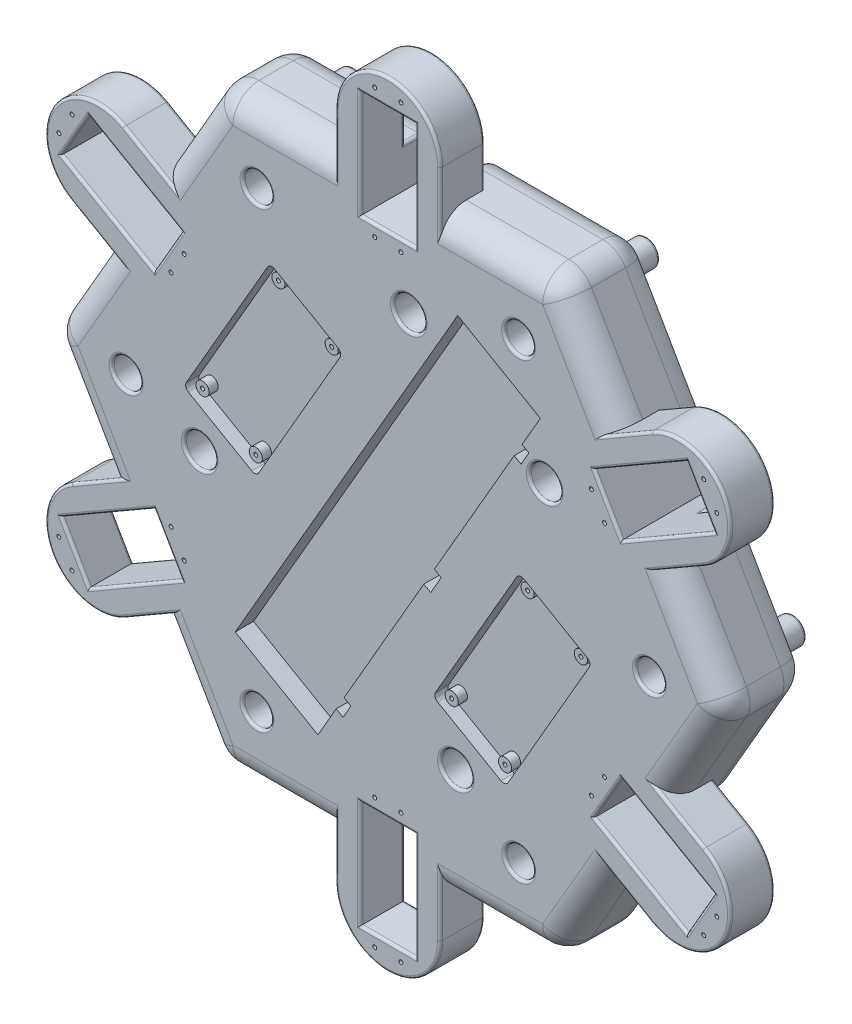
SolidWorks part; units mm, degrees
material "ABS"
ref_plane "Front Plane" through (0, 0, 0) normal (0, 0, 1) x (1, 0, 0)
ref_plane "Top Plane" through (0, 0, 0) normal (0, 1, 0) x (1, 0, 0)
ref_plane "Right Plane" through (0, 0, 0) normal (1, 0, 0) x (0, 0, -1)
sketch "HEXAGON" plane through (0, 0, 0) normal (0, 0, 1) x (1, 0, 0)
  line L96 (102.6779, -47.0398) -> (89.2545, -39.2898)
  line L99 (78.7545, -57.4763) -> (92.1779, -65.2263)
  line L102 (10.5, -112.383) -> (10.5, -96.883)
  line L105 (-10.5, -96.883) -> (-10.5, -112.383)
  line L108 (-78.7545, -57.4763) -> (-92.1779, -65.2263)
  line L111 (-102.6779, -47.0398) -> (-89.2545, -39.2898)
  line L114 (-89.2545, 39.5237) -> (-102.6779, 47.2737)
  line L117 (-78.7545, 57.7102) -> (-92.1779, 65.4602)
  line L148 (-64.9519, -112.383) -> (64.9519, -112.383)
  line L149 (-64.9519, -112.383) -> (-129.9038, 0.117)
  line L150 (-129.9038, 0.117) -> (-64.9519, 112.617)
  line L151 (129.9038, 0.117) -> (64.9519, -112.383)
  line L155 (92.1779, 65.4602) -> (78.7545, 57.7102)
  line L156 (89.2545, 39.5237) -> (102.6779, 47.2737)
  line L157 (78.7545, 57.7102) -> (89.2545, 39.5237)
  line L158 (64.9519, 112.617) -> (129.9038, 0.117)
  line L159 (-10.5, 112.617) -> (-10.5, 97.117)
  line L160 (10.5, 97.117) -> (10.5, 112.617)
  line L161 (10.5, 97.117) -> (-10.5, 97.117)
  line L162 (-64.9519, 112.617) -> (64.9519, 112.617)
  line L163 (89.2545, -39.2898) -> (78.7545, -57.4763)
  line L164 (10.5, -96.883) -> (-10.5, -96.883)
  line L165 (-78.7545, -57.4763) -> (-89.2545, -39.2898)
  line L166 (-89.2545, 39.5237) -> (-78.7545, 57.7102)
extrude "MBODY" add sketch "HEXAGON" along normal blind 33
sketch "BottomFloor" plane through (0, 0, 0) normal (0, 0, 1) x (1, 0, 0)
  line L24 (0, -112.383) -> (20, -112.383)
  line L29 (20, -112.383) -> (20, -82.383)
  line L82 (-87.4279, 73.6875) -> (-67.8387, 107.617)
  line L83 (20, -82.383) -> (-20, -82.383)
  line L84 (-20, -82.383) -> (-20, -112.383)
  line L85 (-20, -112.383) -> (0, -112.383)
  line L87 (97.4279, -56.133) -> (107.4279, -38.8125)
  line L88 (107.4279, -38.8125) -> (81.4471, -23.8125)
  line L89 (81.4471, -23.8125) -> (61.4471, -58.4535)
  line L90 (61.4471, -58.4535) -> (87.4279, -73.4535)
  line L91 (87.4279, -73.4535) -> (97.4279, -56.133)
  line L92 (-97.4279, -56.133) -> (-87.4279, -73.4535)
  line L93 (-87.4279, -73.4535) -> (-61.4471, -58.4535)
  line L94 (-61.4471, -58.4535) -> (-81.4471, -23.8125)
  line L95 (-81.4471, -23.8125) -> (-107.4279, -38.8125)
  line L96 (-107.4279, -38.8125) -> (-97.4279, -56.133)
  line L97 (-97.4279, 56.367) -> (-107.4279, 39.0465)
  line L98 (-107.4279, 39.0465) -> (-81.4471, 24.0465)
  line L99 (-81.4471, 24.0465) -> (-61.4471, 58.6875)
  line L100 (-61.4471, 58.6875) -> (-87.4279, 73.6875)
  line L101 (-87.4279, 73.6875) -> (-97.4279, 56.367)
  line L102 (0, 112.617) -> (20, 112.617)
  line L103 (20, 112.617) -> (20, 82.617)
  line L104 (20, 82.617) -> (-20, 82.617)
  line L105 (-20, 82.617) -> (-20, 112.617)
  line L106 (-20, 112.617) -> (0, 112.617)
  line L107 (97.4279, 56.367) -> (87.4279, 73.6875)
  line L108 (87.4279, 73.6875) -> (61.4471, 58.6875)
  line L109 (61.4471, 58.6875) -> (81.4471, 24.0465)
  line L110 (81.4471, 24.0465) -> (107.4279, 39.0465)
  line L111 (107.4279, 39.0465) -> (97.4279, 56.367)
  line L112 (-59.1784, 112.617) -> (-20, 112.617)
  line L113 (20, 112.617) -> (59.1784, 112.617)
  line L114 (67.8387, 107.617) -> (87.4279, 73.6875)
  line L115 (107.4279, 39.0465) -> (127.0171, 5.117)
  line L116 (127.0171, -4.883) -> (107.4279, -38.8125)
  line L117 (87.4279, -73.4535) -> (67.8387, -107.383)
  line L118 (10.5, -112.383) -> (64.9519, -112.383) construction
  line L119 (59.1784, -112.383) -> (20, -112.383)
  line L120 (-20, -112.383) -> (-59.1784, -112.383)
  line L121 (-67.8387, -107.383) -> (-87.4279, -73.4535)
  line L122 (-107.4279, -38.8125) -> (-127.0171, -4.883)
  line L123 (-127.0171, 5.117) -> (-107.4279, 39.0465)
  line L124 (64.9519, 112.617) -> (59.1784, 102.617)
  line L125 (59.1784, 102.617) -> (56.0184, 97.1437)
  line L126 (129.9038, 0.117) -> (118.3568, 0.117)
  line L127 (118.3568, 0.117) -> (112.0368, 0.117)
  line L128 (-64.9519, 112.617) -> (-59.1784, 102.617)
  line L129 (-59.1784, 102.617) -> (-56.0184, 97.1437)
  line L130 (64.9519, -112.383) -> (59.1784, -102.383)
  line L131 (59.1784, -102.383) -> (56.0184, -96.9098)
  line L132 (-129.9038, 0.117) -> (-118.3568, 0.117)
  line L133 (-118.3568, 0.117) -> (-112.0368, 0.117)
  line L134 (-64.9519, -112.383) -> (-59.1784, -102.383)
  line L135 (-59.1784, -102.383) -> (-56.0184, -96.9098)
  arc A0 (-127.0171, 5.117) -> (-127.0171, -4.883) centre (-118.3568, 0.117) ccw
  arc A1 (-67.8387, -107.383) -> (-59.1784, -112.383) centre (-59.1784, -102.383) ccw
  arc A2 (59.1784, -112.383) -> (67.8387, -107.383) centre (59.1784, -102.383) ccw
  arc A3 (127.0171, -4.883) -> (127.0171, 5.117) centre (118.3568, 0.117) ccw
  arc A4 (67.8387, 107.617) -> (59.1784, 112.617) centre (59.1784, 102.617) ccw
  arc A5 (-59.1784, 112.617) -> (-67.8387, 107.617) centre (-59.1784, 102.617) ccw
  circle A6 centre (-56.0184, -96.9098) radius 5
  circle A7 centre (56.0184, -96.9098) radius 5
  circle A8 centre (112.0368, 0.117) radius 5
  circle A9 centre (56.0184, 97.1437) radius 5
  circle A10 centre (-56.0184, 97.1437) radius 5
  circle A11 centre (-112.0368, 0.117) radius 5
  point P45 (-129.9038, 0.117)
  point P48 (-64.9519, -112.383)
  point P51 (64.9519, -112.383)
  point P54 (129.9038, 0.117)
  point P57 (64.9519, 112.617)
  point P60 (-64.9519, 112.617)
  dimension "D1" = 10
extrude "BODYBASE" add sketch "BottomFloor" against normal blind 10
sketch "CircleBits" plane through (0, 0, 33) normal (0, 0, 1) x (1, 0, 0)
  line L4 (-87.4279, -73.4535) -> (-100.8513, -81.2035)
  line L22 (-20, 112.617) -> (-20, 128.117)
  line L24 (20, 112.617) -> (10.5, 112.617)
  line L26 (10.5, 112.617) -> (10.5, 138.117)
  line L27 (10.5, 138.117) -> (-10.5, 138.117)
  line L28 (-10.5, 138.117) -> (-10.5, 112.617)
  line L43 (-20, 112.617) -> (-10.5, 112.617)
  line L44 (20, -112.383) -> (20, -127.883)
  line L45 (87.4279, 73.6875) -> (100.8513, 81.4375)
  line L46 (107.4279, 39.0465) -> (120.8513, 46.7965)
  line L47 (107.4279, 39.0465) -> (102.6779, 47.2737)
  line L48 (102.6779, 47.2737) -> (124.7615, 60.0237)
  line L49 (124.7615, 60.0237) -> (114.2615, 78.2102)
  line L50 (114.2615, 78.2102) -> (92.1779, 65.4602)
  line L51 (87.4279, 73.6875) -> (92.1779, 65.4602)
  line L52 (-20, -112.383) -> (-20, -127.883)
  line L53 (-20, -112.383) -> (-10.5, -112.383)
  line L54 (-10.5, -112.383) -> (-10.5, -137.883)
  line L55 (-10.5, -137.883) -> (10.5, -137.883)
  line L56 (10.5, -137.883) -> (10.5, -112.383)
  line L57 (20, -112.383) -> (10.5, -112.383)
  line L58 (107.4279, -38.8125) -> (120.8513, -46.5625)
  line L59 (87.4279, -73.4535) -> (100.8513, -81.2035)
  line L60 (87.4279, -73.4535) -> (92.1779, -65.2263)
  line L61 (92.1779, -65.2263) -> (114.2615, -77.9763)
  line L62 (114.2615, -77.9763) -> (124.7615, -59.7898)
  line L63 (124.7615, -59.7898) -> (102.6779, -47.0398)
  line L64 (107.4279, -38.8125) -> (102.6779, -47.0398)
  line L65 (-107.4279, -38.8125) -> (-120.8513, -46.5625)
  line L66 (-107.4279, -38.8125) -> (-102.6779, -47.0398)
  line L67 (-102.6779, -47.0398) -> (-124.7615, -59.7898)
  line L68 (-124.7615, -59.7898) -> (-114.2615, -77.9763)
  line L69 (-114.2615, -77.9763) -> (-92.1779, -65.2263)
  line L70 (-87.4279, -73.4535) -> (-92.1779, -65.2263)
  line L71 (-107.4279, 39.0465) -> (-120.8513, 46.7965)
  line L72 (-87.4279, 73.6875) -> (-100.8513, 81.4375)
  line L73 (-87.4279, 73.6875) -> (-92.1779, 65.4602)
  line L74 (-92.1779, 65.4602) -> (-114.2615, 78.2102)
  line L75 (-114.2615, 78.2102) -> (-124.7615, 60.0237)
  line L76 (-124.7615, 60.0237) -> (-102.6779, 47.2737)
  line L77 (-107.4279, 39.0465) -> (-102.6779, 47.2737)
  line L80 (20, 128.117) -> (20, 112.617)
  arc A6 (100.8513, 81.4375) -> (120.8513, 46.7965) centre (110.8513, 64.117) cw
  arc A7 (20, -127.883) -> (-20, -127.883) centre (0, -127.883) cw
  arc A8 (120.8513, -46.5625) -> (100.8513, -81.2035) centre (110.8513, -63.883) cw
  arc A9 (-100.8513, -81.2035) -> (-120.8513, -46.5625) centre (-110.8513, -63.883) cw
  arc A10 (-120.8513, 46.7965) -> (-100.8513, 81.4375) centre (-110.8513, 64.117) cw
  arc A11 (-20, 128.117) -> (20, 128.117) centre (0, 128.117) cw
extrude "SERVOCIRCLE" add sketch "CircleBits" against normal blind 17
sketch "Breadboard" plane through (0, 0, 33) normal (0, 0, 1) x (1, 0, 0)
  line L1 (-26.695, -82.7372) -> (-58.305, -64.4872)
  line L3 (-58.305, -64.4872) -> (26.695, 82.7372)
  line L4 (58.305, 64.4872) -> (26.695, 82.7372)
  line L5 (58.305, 64.4872) -> (57.305, 62.7551)
  line L6 (57.305, 62.7551) -> (65.9652, 57.7551)
  line L10 (-16.695, -65.4167) -> (13.805, -12.5891)
  line L13 (51.305, 52.3628) -> (53.903, 50.8628)
  line L14 (53.903, 50.8628) -> (50.903, 45.6667)
  line L15 (50.903, 45.6667) -> (48.305, 47.1667)
  line L18 (16.403, -14.0891) -> (13.805, -12.5891)
  line L19 (-16.695, -65.4167) -> (-14.097, -66.9167)
  line L20 (-14.097, -66.9167) -> (-17.097, -72.1128)
  line L21 (-17.097, -72.1128) -> (-19.695, -70.6128)
  line L24 (-26.695, -82.7372) -> (-25.695, -81.0051)
  line L25 (-25.695, -81.0051) -> (-17.0348, -86.0051)
  line L26 (57.305, 62.7551) -> (51.305, 52.3628)
  line L27 (-25.695, -81.0051) -> (-19.695, -70.6128)
  line L29 (20.403, -7.1609) -> (17.805, -5.6609)
  line L30 (17.805, -5.6609) -> (48.305, 47.1667)
  line L31 (16.403, -14.0891) -> (20.403, -7.1609)
  point P0 (-15.805, 9.125)
extrude "BBCUT" cut sketch "Breadboard" against normal blind 7 contours L24 L1 L3 L4 L5 L26 L13 L14 L15 L30 L29 L31 L18 L10 L19 L20 L21 L27
sketch "Sketch9" plane through (0, 0, 33) normal (0, 0, 1) x (1, 0, 0)
  line L5 (76.2298, -5.7892) -> (51.9811, 8.2108)
  line L6 (-43.251, 63.1456) -> (-19.0023, 49.1456)
  line L8 (18.9811, -48.9469) -> (43.2298, -62.9469)
  line L11 (-45.983, 62.4136) -> (-76.983, 8.72)
  line L12 (-76.251, 5.9879) -> (-52.0023, -8.0121)
  line L13 (-18.2702, 46.4136) -> (-49.2702, -7.28)
  line L14 (76.9618, -8.5212) -> (45.9618, -62.2148)
  line L15 (49.249, 7.4788) -> (18.249, -46.2148)
  arc A6 (-76.983, 8.72) -> (-76.251, 5.9879) centre (-75.251, 7.72) ccw
  arc A7 (-52.0023, -8.0121) -> (-49.2702, -7.28) centre (-51.0023, -6.28) ccw
  arc A8 (-18.2702, 46.4136) -> (-19.0023, 49.1456) centre (-20.0023, 47.4136) ccw
  arc A9 (-43.251, 63.1456) -> (-45.983, 62.4136) centre (-44.251, 61.4136) ccw
  arc A10 (18.249, -46.2148) -> (18.9811, -48.9469) centre (19.9811, -47.2148) ccw
  arc A11 (43.2298, -62.9469) -> (45.9618, -62.2148) centre (44.2298, -61.2148) ccw
  arc A12 (76.9618, -8.5212) -> (76.2298, -5.7892) centre (75.2298, -7.5212) ccw
  arc A13 (51.9811, 8.2108) -> (49.249, 7.4788) centre (50.9811, 6.4788) ccw
  point P7 (44.9618, -63.9469)
  point P11 (77.9618, -6.7892)
  dimension "D1" = 2
  dimension "D2" = 2
extrude "PCACUT" cut sketch "Sketch9" against normal blind 5 contours L5 A13 L15 A10 L8 A11 L14 A12 | L11 A6 L12 A7 L13 A8 L6 A9
sketch "Sketch10" plane through (0, 0, 28) normal (0, 0, 1) x (1, 0, 0)
  circle A0 centre (22.9296, -46.6078) radius 0.75
  circle A1 centre (43.2812, -58.3578) radius 0.75
  circle A2 centre (51.9296, 3.6217) radius 0.75
  circle A3 centre (72.2812, -8.1283) radius 0.75
  circle A4 centre (51.9296, 3.6217) radius 2.5
  circle A5 centre (72.2812, -8.1283) radius 2.5
  circle A6 centre (43.2812, -58.3578) radius 2.5
  circle A7 centre (22.9296, -46.6078) radius 2.5
  circle A8 centre (-72.3024, 8.327) radius 0.75
  circle A9 centre (-51.9508, -3.423) radius 0.75
  circle A10 centre (-43.3024, 58.5565) radius 0.75
  circle A11 centre (-22.9508, 46.8065) radius 0.75
  circle A12 centre (-43.3024, 58.5565) radius 2.5
  circle A13 centre (-22.9508, 46.8065) radius 2.5
  circle A14 centre (-51.9508, -3.423) radius 2.5
  circle A15 centre (-72.3024, 8.327) radius 2.5
extrude "PCAFIXTURE" add sketch "Sketch10" along normal blind 3.5 contours A0 | A2 | A4 | A3 | A5 | A1 | A6 | A7 | A12 | A10 | A13 | A11 | A14 | A9 | A15 | A8
sketch "Sketch16" plane through (0, 0, 0) normal (0, 0, -1) x (-1, 0, 0)
  line L0 (-47.6314, -82.383) -> (-61.4471, -58.4535)
  line L1 (-61.4471, -58.4535) -> (-81.4471, -23.8125)
  line L2 (-20, -82.383) -> (-47.6314, -82.383)
  line L3 (81.4471, -23.8125) -> (95.2628, 0.117)
  line L4 (-81.4471, 24.0465) -> (-61.4471, 58.6875)
  line L5 (-20, 82.617) -> (20, 82.617)
  line L6 (61.4471, 58.6875) -> (81.4471, 24.0465)
  line L7 (81.4471, -23.8125) -> (61.4471, -58.4535)
  line L10 (20, -82.383) -> (-20, -82.383)
  line L11 (47.6314, 82.617) -> (20, 82.617)
  line L12 (-20, 82.617) -> (-47.6314, 82.617)
  line L13 (-95.2628, 0.117) -> (-81.4471, -23.8125)
  line L14 (20, -82.383) -> (47.6314, -82.383)
  line L15 (-61.4471, 58.6875) -> (-47.6314, 82.617)
  line L16 (-81.4471, 24.0465) -> (-95.2628, 0.117)
  line L17 (61.4471, 58.6875) -> (47.6314, 82.617)
  line L18 (81.4471, 24.0465) -> (95.2628, 0.117)
  line L19 (61.4471, -58.4535) -> (47.6314, -82.383)
extrude "HOLLOWBOTTOM" cut sketch "Sketch16" against normal blind 18
sketch "Sketch18" plane through (0, 0, 18) normal (0, 0, 1) x (1, 0, 0)
  line L2 (31.3301, 44.3823) -> (37.8253, 40.6323)
  line L3 (37.8253, 40.6323) -> (40.3253, 44.9625)
  line L7 (-10.6699, -28.3638) -> (31.3301, 44.3823)
  line L9 (72.0333, 20.8823) -> (30.0333, -51.8638)
  line L10 (-68.8352, -35.1091) -> (3.9109, -77.1091)
  line L12 (40.3253, 44.9625) -> (47.2535, 40.9625)
  line L17 (-10.6699, -28.3638) -> (-4.1747, -32.1138)
  line L21 (2.7535, -36.1138) -> (0.2535, -40.4439)
  line L22 (0.2535, -40.4439) -> (-6.6747, -36.4439)
  line L23 (-6.6747, -36.4439) -> (-4.1747, -32.1138)
  line L29 (47.2535, 40.9625) -> (44.7535, 36.6323)
  line L30 (72.0333, 20.8823) -> (65.5381, 24.6323)
  line L31 (65.5381, 24.6323) -> (68.0381, 28.9625)
  line L32 (68.0381, 28.9625) -> (61.1099, 32.9625)
  line L33 (61.1099, 32.9625) -> (58.6099, 28.6323)
  line L35 (0, 0.117) -> (-15, -25.8638)
  line L39 (30.0333, -51.8638) -> (23.5381, -48.1138)
  line L40 (23.5381, -48.1138) -> (21.0381, -52.4439)
  line L41 (21.0381, -52.4439) -> (14.1099, -48.4439)
  line L42 (14.1099, -48.4439) -> (16.6099, -44.1138)
  line L43 (16.6099, -44.1138) -> (2.7535, -36.1138)
  line L44 (44.7535, 36.6323) -> (58.6099, 28.6323)
  line L51 (-18.0541, 72.846) -> (-11.5589, 69.096)
  line L52 (-11.5589, 69.096) -> (-9.0589, 73.4262)
  line L53 (-60.0541, 0.0999) -> (-18.0541, 72.846)
  line L54 (22.6491, 49.346) -> (-19.3509, -23.4001)
  line L55 (-9.0589, 73.4262) -> (-2.1307, 69.4262)
  line L56 (-60.0541, 0.0999) -> (-53.5589, -3.6501)
  line L57 (-46.6307, -7.6501) -> (-49.1307, -11.9802)
  line L58 (-49.1307, -11.9802) -> (-56.0589, -7.9802)
  line L59 (-56.0589, -7.9802) -> (-53.5589, -3.6501)
  line L60 (-2.1307, 69.4262) -> (-4.6307, 65.096)
  line L61 (22.6491, 49.346) -> (16.1539, 53.096)
  line L62 (16.1539, 53.096) -> (18.6539, 57.4262)
  line L63 (18.6539, 57.4262) -> (11.7257, 61.4262)
  line L64 (11.7257, 61.4262) -> (9.2257, 57.096)
  line L65 (-19.3509, -23.4001) -> (-25.8461, -19.6501)
  line L66 (-25.8461, -19.6501) -> (-28.3461, -23.9802)
  line L67 (-28.3461, -23.9802) -> (-35.2743, -19.9802)
  line L68 (-35.2743, -19.9802) -> (-32.7743, -15.6501)
  line L69 (-32.7743, -15.6501) -> (-46.6307, -7.6501)
  line L70 (-4.6307, 65.096) -> (9.2257, 57.096)
  line L71 (16.6161, -65.1031) -> (12.2859, -62.6031)
  line L72 (-60.4602, -20.6031) -> (-56.5852, -13.8915)
  line L73 (-64.9602, -28.3974) -> (-68.8352, -35.1091)
  line L74 (-60.4602, -20.6031) -> (-64.7903, -18.1031)
  line L75 (12.2859, -62.6031) -> (16.1609, -55.8915)
  line L76 (-27.4757, -47.5893) -> (-28.4757, -49.3214)
  line L77 (-64.7903, -18.1031) -> (-69.2903, -25.8974)
  line L78 (-69.2903, -25.8974) -> (-64.9602, -28.3974)
  line L81 (16.6161, -65.1031) -> (12.1161, -72.8974)
  line L82 (12.1161, -72.8974) -> (7.7859, -70.3974)
  line L83 (7.7859, -70.3974) -> (3.9109, -77.1091)
  line L84 (47.6314, 82.617) -> (-47.6314, -82.383)
  line L85 (-47.6314, -82.383) -> (-95.2628, 0.117) construction
  line L86 (47.6314, -82.383) -> (-47.6314, -82.383) construction
  line L87 (-71.4471, 41.367) -> (71.4471, -41.133)
  line L88 (-95.2628, 0.117) -> (-47.6314, 82.617) construction
  line L89 (95.2628, 0.117) -> (47.6314, -82.383) construction
  line L90 (16.1609, -55.8915) -> (-56.5852, -13.8915)
  point P73 (-67.0403, -22.0003)
  point P78 (14.3661, -69.0003)
extrude "BOTTOMBATTCUT" cut sketch "Sketch18" along normal blind 2 contours L81 L82 L83 L10 L73 L78 L77 L74 L72 L90 L75 L71 | L51 L52 L55 L60 L70 L64 L63 L62 L61 L54 L65 L66 L67 L68 L69 L57 L58 L59 L56 L53 | L2 L3 L12 L29 L44 L33 L32 L31 L30 L9 L39 L40 L41 L42 L43 L21 L22 L23 L17 L7
sketch "Sketch20" plane through (0, 0, 20) normal (0, 0, -1) x (-1, 0, 0)
  line L0 (-30.6817, -3.7407) -> (-48.0022, -13.7407)
  line L1 (30.8371, -53.2945) -> (6.6534, -67.257)
  line L2 (-23.2676, -63.7472) -> (-11.4832, -56.9435)
  line L3 (20.4621, -35.3245) -> (32.4621, -56.1091)
  line L4 (67.0403, -22.0003) -> (-14.3661, -69.0003)
  line L5 (-30.6817, -3.7407) -> (-13.3612, 6.2593)
  line L6 (64.7903, -18.1031) -> (69.2903, -25.8974) construction
  line L7 (-48.0022, -13.7407) -> (-61.9647, 10.443)
  line L8 (-13.3612, 6.2593) -> (0.6013, -17.9245)
  line L9 (-13.3612, 6.2593) -> (-27.3237, 30.443)
  line L10 (-27.3237, 30.443) -> (-32.5987, 39.5796)
  line L11 (30.8371, -53.2945) -> (21.8371, -37.706)
  line L12 (21.8371, -37.706) -> (46.0209, -23.7435)
  line L13 (-16.6161, -65.1031) -> (-12.1161, -72.8974) construction
  line L15 (18.7025, 24.723) -> (1.382, 14.723)
  line L16 (18.7025, 24.723) -> (36.023, 34.723)
  line L17 (1.382, 14.723) -> (-12.5805, 38.9067)
  line L18 (36.023, 34.723) -> (49.9855, 10.5392)
  line L19 (36.023, 34.723) -> (22.0605, 58.9067)
  line L20 (22.0605, 58.9067) -> (16.7855, 68.0433)
  line L22 (21.8371, -37.706) -> (-23.2676, -63.7472)
  line L23 (68.8352, -35.1091) -> (-3.9109, -77.1091) construction
  line L24 (39.7025, -11.6501) -> (-2.2975, 61.096)
  line L25 (32.7743, -15.6501) -> (46.6307, -7.6501) construction
  line L26 (4.6307, 65.096) -> (-9.2257, 57.096) construction
  line L27 (-51.6817, 32.6323) -> (-9.6817, -40.1138)
  line L28 (-44.7535, 36.6323) -> (-58.6099, 28.6323) construction
  line L29 (-16.6099, -44.1138) -> (-2.7535, -36.1138) construction
  line L30 (-51.0333, -15.4907) -> (-10.3301, 8.0093)
  line L31 (-72.0333, 20.8823) -> (-30.0333, -51.8638) construction
  line L32 (10.6699, -28.3638) -> (-31.3301, 44.3823) construction
  line L33 (-1.6491, 12.973) -> (39.0541, 36.473)
  line L34 (-22.6491, 49.346) -> (19.3509, -23.4001) construction
  line L35 (60.0541, 0.0999) -> (18.0541, 72.846) construction
  circle A0 centre (0.6013, -17.9245) radius 2
  circle A1 centre (-61.9647, 10.443) radius 2
  circle A2 centre (-32.5987, 39.5796) radius 0.8
  circle A3 centre (49.9855, 10.5392) radius 2
  circle A4 centre (-12.5805, 38.9067) radius 2
  circle A5 centre (16.7855, 68.0433) radius 0.8
  circle A6 centre (-11.4832, -56.9435) radius 0.8
  circle A7 centre (6.6534, -67.257) radius 2
  circle A8 centre (46.0209, -23.7435) radius 2
extrude "BOTTOMBATTFIXTURE" cut sketch "Sketch20" against normal blind 3.45 contours A6 | A7 | A0 | A1 | A2 | A8 | A5 | A4 | A3
sketch "Sketch33" plane through (0, 0, 20) normal (0, 0, -1) x (1, 0, 0)
  line L0 (30.6817, 3.7407) -> (48.0022, 13.7407)
  line L1 (-30.8371, 53.2945) -> (-6.6534, 67.257)
  line L2 (23.2676, 63.7472) -> (11.4832, 56.9435)
  line L3 (-20.4621, 35.3245) -> (-32.2121, 55.6761)
  line L4 (-66.6073, 22.2503) -> (13.9331, 68.7503)
  line L5 (30.6817, 3.7407) -> (13.3612, -6.2593)
  line L6 (48.0022, 13.7407) -> (61.9647, -10.443)
  line L7 (13.3612, -6.2593) -> (-0.6013, 17.9245)
  line L8 (13.3612, -6.2593) -> (27.3237, -30.443)
  line L9 (27.3237, -30.443) -> (32.5987, -39.5796)
  line L10 (-30.8371, 53.2945) -> (-21.8371, 37.706)
  line L11 (-21.8371, 37.706) -> (-46.0209, 23.7435)
  line L12 (-18.7025, -24.723) -> (-1.382, -14.723)
  line L13 (-18.7025, -24.723) -> (-36.023, -34.723)
  line L14 (-1.382, -14.723) -> (12.5805, -38.9067)
  line L15 (-36.023, -34.723) -> (-49.9855, -10.5392)
  line L16 (-36.023, -34.723) -> (-22.0605, -58.9067)
  line L17 (-22.0605, -58.9067) -> (-16.7855, -68.0433)
  line L18 (-21.8371, 37.706) -> (23.2676, 63.7472)
  line L19 (-39.4525, 11.2171) -> (2.0475, -60.663)
  line L20 (51.4317, -32.1993) -> (9.9317, 39.6808)
  line L21 (50.6003, 15.2407) -> (10.7631, -7.7593)
  line L22 (1.2161, -13.223) -> (-38.6211, -36.223)
  circle A0 centre (-0.6013, 17.9245) radius 2
  circle A1 centre (61.9647, -10.443) radius 2
  circle A2 centre (32.5987, -39.5796) radius 0.785
  circle A3 centre (-49.9855, -10.5392) radius 2
  circle A4 centre (12.5805, -38.9067) radius 2
  circle A5 centre (-16.7855, -68.0433) radius 0.785
  circle A6 centre (11.4832, 56.9435) radius 0.785
  circle A7 centre (-6.6534, 67.257) radius 2
  circle A8 centre (-46.0209, 23.7435) radius 2
  circle A9 centre (-6.6534, 67.257) radius 1.5
  circle A10 centre (-46.0209, 23.7435) radius 1.5
  circle A11 centre (-49.9855, -10.5392) radius 1.5
  circle A12 centre (12.5805, -38.9067) radius 1.5
  circle A13 centre (61.9647, -10.443) radius 1.5
  circle A14 centre (-0.6013, 17.9245) radius 1.5
extrude "BOTTOMBATTFIXTURE1" add sketch "Sketch33" against normal blind 1.75 contours A8 | A10 | A3 | A11 | A4 | A12 | A1 | A13 | A0 | A14 | A7 | A9
fillet "BOTTOMBATTFIXTURE2" radius 0.8 6 edges at (11.0805, 38.9067, 20) (60.4647, 10.443, 20) (-51.4855, 10.5392, 20) (-2.1013, -17.9245, 20) (-47.5209, -23.7435, 20) (-8.1534, -67.257, 20)
sketch "Sketch26" plane through (0, 0, 33) normal (0, 0, 1) x (1, 0, 0)
  line L0 (5, -142.133) -> (5, -137.383)
  line L1 (114.2615, 78.2102) -> (89.2545, 39.5237)
  line L2 (-5, -137.383) -> (-5, -142.133)
  line L3 (-5, -142.133) -> (5, -142.133)
  line L4 (5, -92.633) -> (-5, -92.633)
  line L5 (114.2615, -77.9763) -> (89.2545, -39.2898)
  line L6 (5, -97.383) -> (5, -92.633)
  line L7 (-5, -97.383) -> (-10, -97.383)
  line L8 (10.5, -96.883) -> (-10.5, -137.883)
  line L9 (-5, -97.383) -> (-5, -92.633)
  line L10 (125.6921, -66.6779) -> (121.5785, -64.3029)
  line L11 (116.5785, -72.9632) -> (120.6921, -75.3382)
  line L12 (120.6921, -75.3382) -> (125.6921, -66.6779)
  line L13 (82.8239, -41.9279) -> (77.8239, -50.5882)
  line L14 (86.9375, -44.3029) -> (82.8239, -41.9279)
  line L15 (81.9375, -52.9632) -> (79.4375, -57.2933)
  line L16 (81.9375, -52.9632) -> (77.8239, -50.5882)
  line L17 (120.6921, 75.5721) -> (116.5785, 73.1971)
  line L18 (121.5785, 64.5368) -> (125.6921, 66.9118)
  line L19 (125.6921, 66.9118) -> (120.6921, 75.5721)
  line L20 (77.8239, 50.8221) -> (82.8239, 42.1618)
  line L21 (-78.7545, -57.4763) -> (-124.7615, -59.7898)
  line L22 (86.9375, 44.5368) -> (89.4375, 40.2067)
  line L23 (86.9375, 44.5368) -> (82.8239, 42.1618)
  line L24 (-5, 142.367) -> (-5, 137.617)
  line L25 (5, 137.617) -> (5, 142.367)
  line L26 (5, 142.367) -> (-5, 142.367)
  line L27 (-5, 92.867) -> (5, 92.867)
  line L28 (-5, 97.617) -> (-5, 92.867)
  line L29 (5, 97.617) -> (10, 97.617)
  line L30 (5, 97.617) -> (5, 92.867)
  line L31 (-125.6921, 66.9118) -> (-121.5785, 64.5368)
  line L32 (-116.5785, 73.1971) -> (-120.6921, 75.5721)
  line L33 (-120.6921, 75.5721) -> (-125.6921, 66.9118)
  line L34 (-82.8239, 42.1618) -> (-77.8239, 50.8221)
  line L35 (-86.9375, 44.5368) -> (-82.8239, 42.1618)
  line L36 (-81.9375, 53.1971) -> (-79.4375, 57.5272)
  line L37 (-81.9375, 53.1971) -> (-77.8239, 50.8221)
  line L38 (-120.6921, -75.3382) -> (-116.5785, -72.9632)
  line L39 (-121.5785, -64.3029) -> (-125.6921, -66.6779)
  line L40 (-125.6921, -66.6779) -> (-120.6921, -75.3382)
  line L41 (-77.8239, -50.5882) -> (-82.8239, -41.9279)
  line L42 (-81.9375, -52.9632) -> (-77.8239, -50.5882)
  line L43 (-86.9375, -44.3029) -> (-89.4375, -39.9728)
  line L44 (-86.9375, -44.3029) -> (-82.8239, -41.9279)
  line L45 (-89.2545, 39.5237) -> (-114.2615, 78.2102)
  line L46 (77.8239, 50.8221) -> (125.6921, 66.9118)
  line L47 (77.8239, -50.5882) -> (125.6921, -66.6779)
  line L48 (-5, -92.633) -> (5, -142.133)
  line L49 (-82.8239, -41.9279) -> (-120.6921, -75.3382)
  line L50 (-125.6921, 66.9118) -> (-77.8239, 50.8221)
  line L51 (101.758, 58.867) -> (99.9279, 62.0368)
  line L52 (101.758, -58.633) -> (99.9279, -61.8029)
  line L53 (0, -117.383) -> (-3.3849, -117.383)
  line L54 (-101.758, -58.633) -> (-103.7411, -55.4995)
  line L55 (-101.758, 58.867) -> (-99.3191, 62.0406)
  circle A24 centre (-125.6921, -66.6779) radius 0.75
  circle A25 centre (-120.6921, -75.3382) radius 0.75
  circle A26 centre (-82.8239, -41.9279) radius 0.75
  circle A27 centre (-77.8239, -50.5882) radius 0.75
  circle A28 centre (-5, -92.633) radius 0.75
  circle A29 centre (5, -92.633) radius 0.75
  circle A30 centre (-5, -142.133) radius 0.75
  circle A31 centre (5, -142.133) radius 0.75
  circle A32 centre (125.6921, -66.6779) radius 0.75
  circle A33 centre (120.6921, -75.3382) radius 0.75
  circle A34 centre (77.8239, -50.5882) radius 0.75
  circle A35 centre (82.8239, -41.9279) radius 0.75
  circle A36 centre (125.6921, 66.9118) radius 0.75
  circle A37 centre (120.6921, 75.5721) radius 0.75
  circle A38 centre (77.8239, 50.8221) radius 0.75
  circle A39 centre (82.8239, 42.1618) radius 0.75
  circle A40 centre (5, 92.867) radius 0.75
  circle A41 centre (-5, 92.867) radius 0.75
  circle A42 centre (5, 142.367) radius 0.75
  circle A43 centre (-5, 142.367) radius 0.75
  circle A45 centre (-125.6921, 66.9118) radius 0.75
  circle A46 centre (-77.8239, 50.8221) radius 0.75
  circle A47 centre (-82.8239, 42.1618) radius 0.75
  circle A48 centre (-120.6921, 75.5721) radius 0.75
sketch "Sketch28" plane through (0, 0, 18) normal (0, 0, -1) x (-1, 0, 0)
  line L6 (-19.1382, -69.7347) -> (-27.7984, -74.7347)
  line L7 (65.0624, -9.5745) -> (73.7227, -4.5745)
  line L11 (-27.7984, -74.7347) -> (-32.7984, -66.0745)
  line L12 (-32.7984, -66.0745) -> (-24.1382, -61.0745)
  line L14 (78.7227, -13.2347) -> (70.0624, -18.2347)
  line L15 (70.0624, -18.2347) -> (65.0624, -9.5745)
  line L22 (-6.1684, 80.8005) -> (-14.8286, 75.8005)
  line L23 (-14.8286, 75.8005) -> (-9.8286, 67.1403)
  line L24 (-1.1684, 72.1403) -> (-9.8286, 67.1403)
  line L27 (-58.1506, 50.8368) -> (-66.8109, 45.8368)
  line L28 (-66.8109, 45.8368) -> (-61.8109, 37.1766)
  line L29 (-53.1506, 42.1766) -> (-61.8109, 37.1766)
  circle A0 centre (-7.9985, 73.9704) radius 6
  circle A1 centre (-59.9599, 43.9705) radius 6
  circle A2 centre (-25.9683, -67.9046) radius 6
  circle A3 centre (71.8926, -11.4046) radius 6
extrude "CABLEHOLES" cut sketch "Sketch28" against normal blind 15 contours A0 | A1 | A3 | A2
extrude "SERVOSCREWS" cut sketch "Sketch26" against normal blind 3 contours A30 | A31 | A29 | A28 | A27 | A26 | A24 | A25 | A33 | A32 | A35 | A34 | A39 | A38 | A36 | A37 | A40 | A41 | A43 | A42 | A48 | A45 | A47 | A46
sketch "Sketch34" plane through (0, 0, 33) normal (0, 0, 1) x (1, 0, 0)
  line L139 (0, 0) -> (-49.9493, 86.6318)
  line L140 (0, 0) -> (49.9493, 86.6318)
  line L141 (0, 0) -> (50.0506, -86.5733)
  line L142 (0, 0) -> (100, 0)
  line L143 (0, 0) -> (-50.0506, -86.5733)
  line L144 (0, 0) -> (-100, 0)
  circle A14 centre (0, 0) radius 100
  circle A15 centre (-49.9493, 86.6318) radius 5.5
  circle A16 centre (49.9493, 86.6318) radius 5.5
  circle A17 centre (100, 0) radius 5.5
  circle A18 centre (50.0506, -86.5733) radius 5.5
  circle A19 centre (-50.0506, -86.5733) radius 5.5
  circle A20 centre (-100, 0) radius 5.5
extrude "CAPCUTIN" cut sketch "Sketch34" against normal blind 10 contours A18 | A17 | A16 | A15 | A20 | A19
fillet "ROUNDEDGES10MM" radius 10 36 edges at (-76.1899, -92.9183, 33) (64.9519, -112.383, 16.5) (-64.9519, -112.383, 16.5) (-37.726, -112.383, 0) (-42.476, -112.383, 33) (37.726, -112.383, 0) (42.476, -112.383, 33) (-116.2908, 23.6953, 0) (-118.6658, 19.5817, 33) (-129.9038, 0.117, 16.5) (-116.2908, -23.4614, 0) (-118.6658, -19.3478, 33) (-64.9519, 112.617, 16.5) (-78.5649, 89.0386, 0) (-76.1899, 93.1522, 33) (-42.476, 112.617, 33) (-37.726, 112.617, 0) (37.726, 112.617, 0) (42.476, 112.617, 33) (64.9519, 112.617, 16.5) (78.5649, 89.0386, 0) (76.1899, 93.1522, 33) (116.2908, 23.6953, 0) (116.2908, -23.4614, 0) (129.9038, 0.117, 16.5) (118.6658, 19.5817, 33) (118.6658, -19.3478, 33) (-78.5649, -88.8047, 0) (78.5649, -88.8047, 0) (76.1899, -92.9183, 33) (0, 82.617, 0) (-71.4471, 41.367, 0) (71.4471, 41.367, 0) (71.4471, -41.133, 0) (-71.4471, -41.133, 0) (0, -82.383, 0)
fillet "ROUNDEDGES1MM" radius 1 146 edges at (-119.5115, 69.117, 33) (-119.5115, 69.117, 16) (0, 138.117, 16) (0, 138.117, 33) (-119.5115, -68.883, 16) (-119.5115, -68.883, 33) (119.5115, 69.117, 33) (119.5115, 69.117, 16) (0, -137.883, 33) (0, -137.883, 16) (119.5115, -68.883, 33) (119.5115, -68.883, 16) (-10.5, 117.617, 33) (-10.5, 125.367, 16) (-10.5, 112.617, 13) (-10.5, 109.688, 2.9289) (-10.5, 99.867, 0) (-103.2197, 71.8352, 16) (-96.508, 67.9602, 33) (-81.136, 59.0852, 0) (-89.6413, 63.9958, 2.9289) (-92.1779, 65.4602, 13) (-107.008, 49.7737, 33) (-113.7197, 53.6487, 16) (-102.6779, 47.2737, 13) (-100.1413, 45.8092, 2.9289) (-91.636, 40.8987, 0) (-84.0045, 48.617, 0) (-84.0045, 48.617, 33) (0, 97.117, 0) (0, 97.117, 33) (10.5, 125.367, 16) (10.5, 117.617, 33) (10.5, 99.867, 0) (10.5, 109.688, 2.9289) (10.5, 112.617, 13) (113.7197, 53.6487, 16) (107.008, 49.7737, 33) (91.636, 40.8987, 0) (100.1413, 45.8092, 2.9289) (102.6779, 47.2737, 13) (-96.508, -67.7263, 33) (-103.2197, -71.6013, 16) (-92.1779, -65.2263, 13) (-89.6413, -63.7618, 2.9289) (-81.136, -58.8513, 0) (84.0045, 48.617, 0) (84.0045, 48.617, 33) (-10.5, -125.133, 16) (-10.5, -117.383, 33) (-10.5, -99.633, 0) (-10.5, -109.4541, 2.9289) (-10.5, -112.383, 13) (-113.7197, -53.4148, 16) (-107.008, -49.5398, 33) (-91.636, -40.6648, 0) (-100.1413, -45.5753, 2.9289) (-102.6779, -47.0398, 13) (-84.0045, -48.383, 0) (-84.0045, -48.383, 33) (96.508, 67.9602, 33) (103.2197, 71.8352, 16) (92.1779, 65.4602, 13) (89.6413, 63.9958, 2.9289) (81.136, 59.0852, 0) (0, -96.883, 0) (0, -96.883, 33) (10.5, -117.383, 33) (10.5, -125.133, 16) (10.5, -112.383, 13) (10.5, -109.4541, 2.9289) (10.5, -99.633, 0) (103.2197, -71.6013, 16) (96.508, -67.7263, 33) (81.136, -58.8513, 0) (89.6413, -63.7618, 2.9289) (92.1779, -65.2263, 13) (84.0045, -48.383, 0) (84.0045, -48.383, 33) (107.008, -49.5398, 33) (113.7197, -53.4148, 16) (102.6779, -47.0398, 13) (100.1413, -45.5753, 2.9289) (91.636, -40.6648, 0) (19.9683, -67.9046, 18) (19.9683, -67.9046, 33) (53.9599, 43.9705, 18) (53.9599, 43.9705, 33) (1.9985, 73.9704, 18) (1.9985, 73.9704, 33) (-77.8926, -11.4046, 18) (-77.8926, -11.4046, 33) (-51.0184, -96.9098, -10) (61.0184, -96.9098, -10) (117.0368, 0.117, -10) (61.0184, 97.1437, -10) (-51.0184, 97.1437, -10) (-107.0368, 0.117, -10) (-128.1718, 74.117, 33) (-128.1718, 74.117, 16) (-89.8094, 75.0625, 33) (-20, 115.367, 33) (89.8094, 75.0625, 33) (128.1718, 74.117, 33) (128.1718, 74.117, 16) (109.8094, 40.4215, 33) (109.8094, -40.1875, 33) (128.1718, -73.883, 33) (128.1718, -73.883, 16) (89.8094, -74.8285, 33) (94.1396, -77.3285, 16) (20, -115.133, 33) (0, -147.883, 33) (0, -147.883, 16) (-20, -115.133, 33) (-89.8094, -74.8285, 33) (-128.1718, -73.883, 33) (-128.1718, -73.883, 16) (-109.8094, -40.1875, 33) (-109.8094, 40.4215, 33) (-20, 120.367, 16) (114.1396, 42.9215, 16) (94.1396, 77.5625, 16) (114.1396, -42.6875, 16) (-20, -120.133, 16) (20, -120.133, 16) (-114.1396, -42.6875, 16) (-94.1396, -77.3285, 16) (-94.1396, 77.5625, 16) (-114.1396, 42.9215, 16) (-44.5506, -86.5733, 23) (-44.5506, -86.5733, 33) (55.5506, -86.5733, 23) (55.5506, -86.5733, 33) (105.5, 0, 23) (105.5, 0, 33) (55.4493, 86.6318, 23) (55.4493, 86.6318, 33) (-44.4493, 86.6318, 23) (-44.4493, 86.6318, 33) (-94.5, 0, 23) (-94.5, 0, 33) (20, 120.367, 16) (20, 115.367, 33) (0, 148.117, 16) (0, 148.117, 33)
